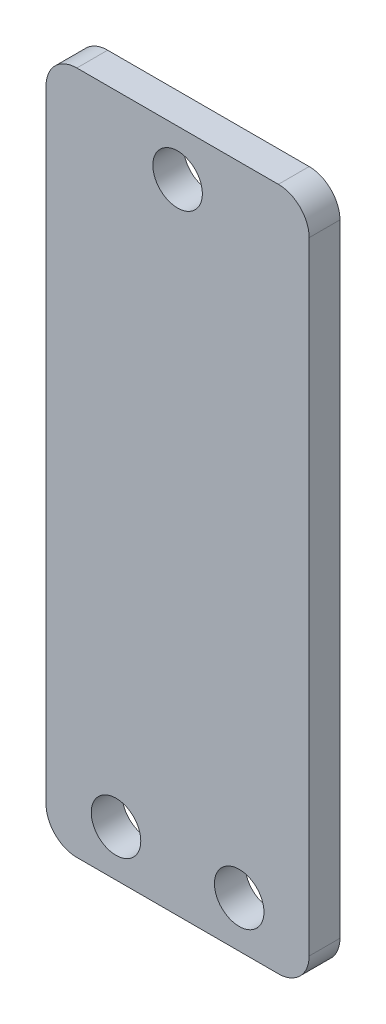
SolidWorks part; units mm, degrees
ref_plane "Front Plane" through (0, 0, 0) normal (0, 0, 1) x (1, 0, 0)
ref_plane "Top Plane" through (0, 0, 0) normal (0, 1, 0) x (1, 0, 0)
ref_plane "Right Plane" through (0, 0, 0) normal (1, 0, 0) x (0, 0, -1)
sketch "Sketch1" plane through (0, 0, 0) normal (0, 0, 1) x (1, 0, 0)
  line L0 (8.9027, -4.6609) -> (-8.9027, -4.6609) construction
  line L1 (10.3886, -4.6609) -> (-10.3886, -4.6609)
  line L2 (13.5636, -1.4859) -> (13.5636, 62.6618)
  line L3 (10.3886, 65.8368) -> (-10.3886, 65.8368)
  line L4 (-13.5636, -1.4859) -> (-13.5636, 62.6618)
  line L5 (72.2623, 65.8368) -> (27.8123, 65.8368) construction
  arc A0 (8.9027, -4.6609) -> (8.9027, 4.6609) centre (8.9027, 0) ccw construction
  arc A1 (-8.9027, 4.6609) -> (-8.9027, -4.6609) centre (-8.9027, 0) ccw construction
  arc A2 (13.5636, 62.6618) -> (10.3886, 65.8368) centre (10.3886, 62.6618) ccw
  arc A3 (-10.3886, 65.8368) -> (-13.5636, 62.6618) centre (-10.3886, 62.6618) ccw
  arc A4 (-10.3886, -4.6609) -> (-13.5636, -1.4859) centre (-10.3886, -1.4859) cw
  arc A5 (10.3886, -4.6609) -> (13.5636, -1.4859) centre (10.3886, -1.4859) ccw
  dimension "D1" = 3.175
extrude "Boss-Extrude1" add sketch "Sketch1" along normal blind 3.175
hole_wizard "#10 Clearance Hole1" positions "Sketch2" profile "Sketch3" hole size "#10" standard "ANSI Inch" end condition through all
sketch "Sketch2" plane through (0, 0, 3.175) normal (0, 0, 1) x (1, 0, 0)
  line L0 (6.35, 0.1016) -> (-6.35, 0.1016) construction
  line L2 (-10.3886, -4.6609) -> (10.3886, -4.6609) construction
  line L3 (10.3886, 65.8368) -> (-10.3886, 65.8368) construction
  point P0 (6.35, 0.1016)
  point P2 (-6.35, 0.1016)
  point P4 (0, 61.0743)
  point P11 (0, 0.1016)
  point P14 (0, -4.6609)
  point P18 (0, 65.8368)
  dimension "D1" = 12.7
  dimension "D2" = 4.7625
  dimension "D3" = 4.7625
sketch "Sketch3" plane through (6.35, 0.1016, 3.175) normal (1, 0, 0) x (0, -1, 0)
  line L0 (0, 0) -> (0, 3.175)
  line L1 (0, 3.175) -> (2.5527, 3.175)
  line L2 (2.5527, 3.175) -> (2.5527, 0)
  line L5 (2.5527, 0) -> (0, 0)
  line L11 (0, -6.35) -> (0, 107.95) construction
  dimension "Thru Hole Dia." = 5.1054
  dimension "Thru Hole Depth" = 3.175
